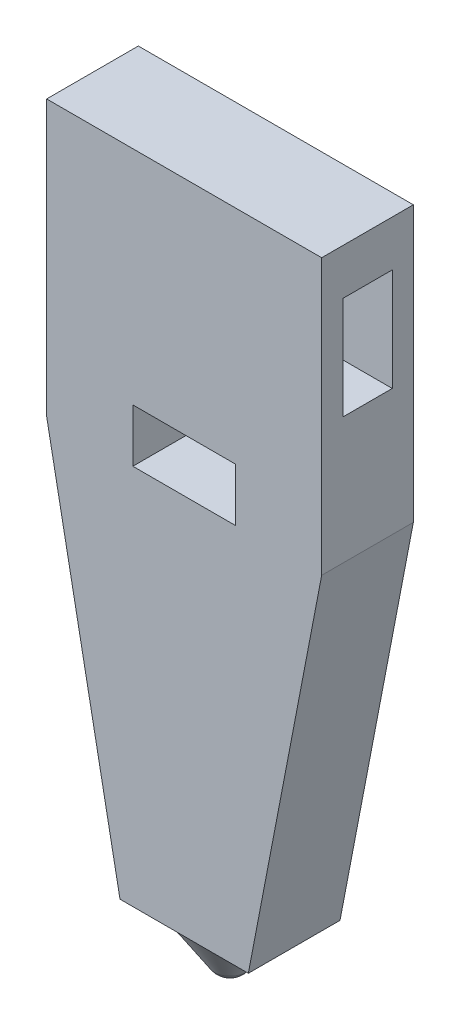
SolidWorks part; units mm, degrees
ref_plane "Front Plane" through (0, 0, 0) normal (0, 0, 1) x (1, 0, 0)
ref_plane "Top Plane" through (0, 0, 0) normal (0, 1, 0) x (1, 0, 0)
ref_plane "Right Plane" through (0, 0, 0) normal (1, 0, 0) x (0, 0, -1)
sketch "Sketch1" plane through (0, 0, 0) normal (0, 0, 1) x (1, 0, 0)
  line L0 (0, -19.05) -> (5.08, -45.466)
  line L1 (0, 0) -> (19.05, 0)
  line L2 (0, 0) -> (0, -19.05)
  line L4 (19.05, 0) -> (19.05, -19.05)
  line L5 (5.08, -45.466) -> (13.97, -45.466)
  line L6 (13.97, -45.466) -> (19.05, -19.05)
  line L7 (9.525, -45.466) -> (9.525, 0) construction
  point P5 (0, 0)
  point P10 (12.7, -12.7)
  point P11 (0, 0)
  point P12 (0, 0)
  dimension "D1" = 19.05
  dimension "D2" = 45.466
  dimension "D3" = 8.89
extrude "Boss-Extrude1" add sketch "Sketch1" along normal blind 6.35
ref_plane "Plane1" through (0, 0, 3.175) normal (0, 0, 1) x (1, 0, 0)
sketch "Sketch2" plane through (0, 0, 3.175) normal (0, 0, 1) x (1, 0, 0)
  line L0 (9.525, -45.466) -> (12.7, -45.466)
  line L1 (12.7, -45.466) -> (10.5884, -48.7003)
  line L2 (9.525, -49.276) -> (9.525, -45.466)
  line L3 (5.08, -45.466) -> (13.97, -45.466) construction
  line L4 (9.525, -49.276) -> (11.1048, -49.276) construction
  arc A0 (10.5884, -48.7003) -> (9.525, -49.276) centre (9.525, -48.006) cw
  point P7 (9.525, -45.466)
  dimension "D2" = 1.27
  dimension "D1" = 3.81
  dimension "D3" = 3.175
revolve "Revolve1" add sketch "Sketch2" angle 360 about L2
sketch "Sketch3" plane through (0, 0, 0) normal (-1, 0, 0) x (0, 0, 1)
  line L0 (6.35, 0) -> (0, 0) construction
  line L1 (1.4605, -3.175) -> (4.8895, -3.175)
  line L2 (1.4605, -3.175) -> (1.4605, -10.287)
  line L3 (1.4605, -10.287) -> (4.8895, -10.287)
  line L4 (4.8895, -3.175) -> (4.8895, -10.287)
  point P6 (3.175, -3.175)
  point P7 (3.175, 0)
  dimension "D1" = 3.175
  dimension "D2" = 3.429
  dimension "D3" = 7.112
extrude "Cut-Extrude1" cut sketch "Sketch3" against normal through all
sketch "Sketch4" plane through (0, 0, 6.35) normal (0, 0, 1) x (1, 0, 0)
  line L0 (19.05, 0) -> (0, 0) construction
  line L1 (5.969, -19.05) -> (13.081, -19.05)
  line L2 (5.969, -19.05) -> (5.969, -15.367)
  line L3 (5.969, -15.367) -> (13.081, -15.367)
  line L4 (13.081, -19.05) -> (13.081, -15.367)
  point P4 (9.525, -15.367)
  point P8 (9.525, 0)
  dimension "D1" = 3.683
  dimension "D2" = 7.112
extrude "Cut-Extrude2" cut sketch "Sketch4" against normal through all
